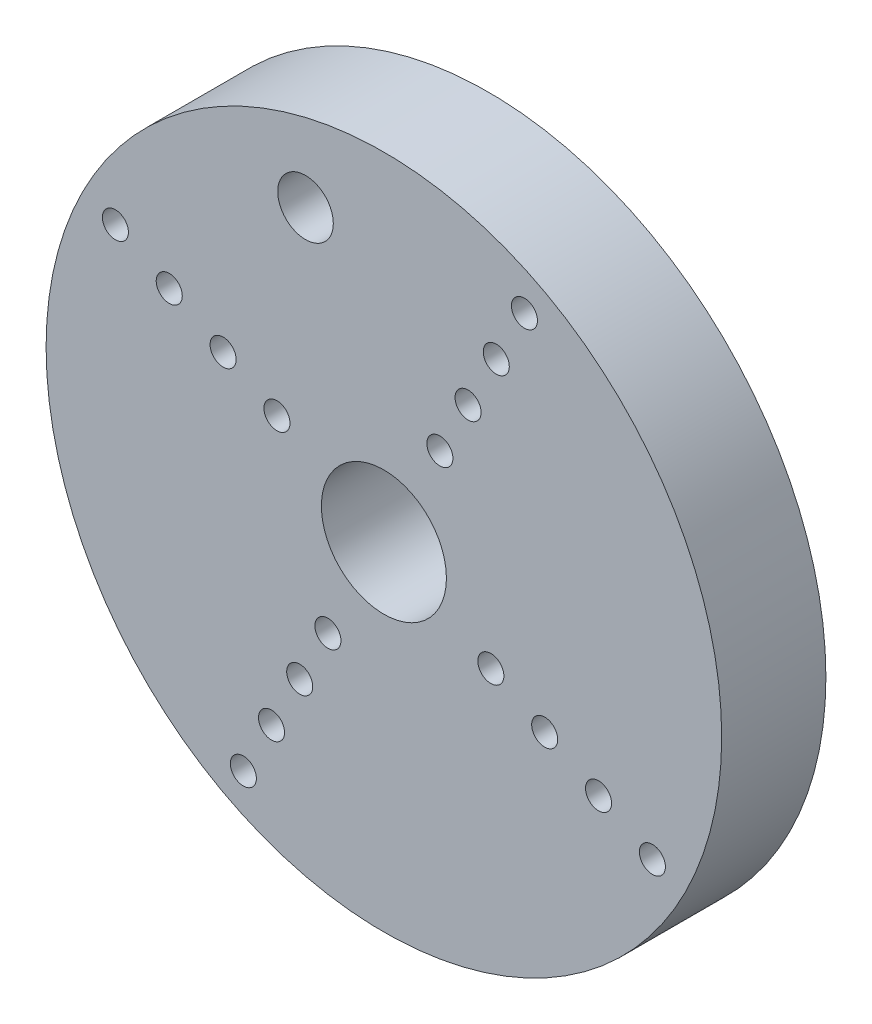
SolidWorks part; units mm, degrees
ref_plane "Front Plane" through (0, 0, 0) normal (0, 0, 1) x (1, 0, 0)
ref_plane "Top Plane" through (0, 0, 0) normal (0, 1, 0) x (1, 0, 0)
ref_plane "Right Plane" through (0, 0, 0) normal (1, 0, 0) x (0, 0, -1)
sketch "Sketch1" plane through (0, 0, 0) normal (0, 0, 1) x (1, 0, 0)
  line L0 (200.7699, 115.2317) -> (224.3227, 122.5986) construction
  line L1 (212.5463, 118.9152) -> (211.7174, 121.5655) construction
  circle A0 centre (224.3227, 122.5986) radius 0.75
  circle A1 centre (222.6995, 119.4978) radius 0.75
  circle A2 centre (221.0763, 116.397) radius 0.75
  circle A3 centre (219.453, 113.2962) radius 0.75
  circle A4 centre (231.6896, 99.0459) radius 0.75
  circle A5 centre (228.5888, 100.6691) radius 0.75
  circle A6 centre (225.488, 102.2923) radius 0.75
  circle A7 centre (222.3871, 103.9155) radius 0.75
  circle A8 centre (208.1368, 91.679) radius 0.75
  circle A9 centre (209.7601, 94.7798) radius 0.75
  circle A10 centre (211.3833, 97.8806) radius 0.75
  circle A11 centre (213.0065, 100.9814) radius 0.75
  circle A12 centre (200.7699, 115.2317) radius 0.75
  circle A13 centre (203.8707, 113.6085) radius 0.75
  circle A14 centre (206.9716, 111.9853) radius 0.75
  circle A15 centre (210.0724, 110.3621) radius 0.75
  circle A16 centre (216.2298, 107.1388) radius 3.6
  circle A17 centre (216.2298, 107.1388) radius 19.45
  circle A18 centre (211.7174, 121.5655) radius 1.6
  point P42 (216.2298, 107.1388)
  dimension "D1" = 4
extrude "Boss-Extrude1" add sketch "Sketch1" along normal blind 6 contours A17
